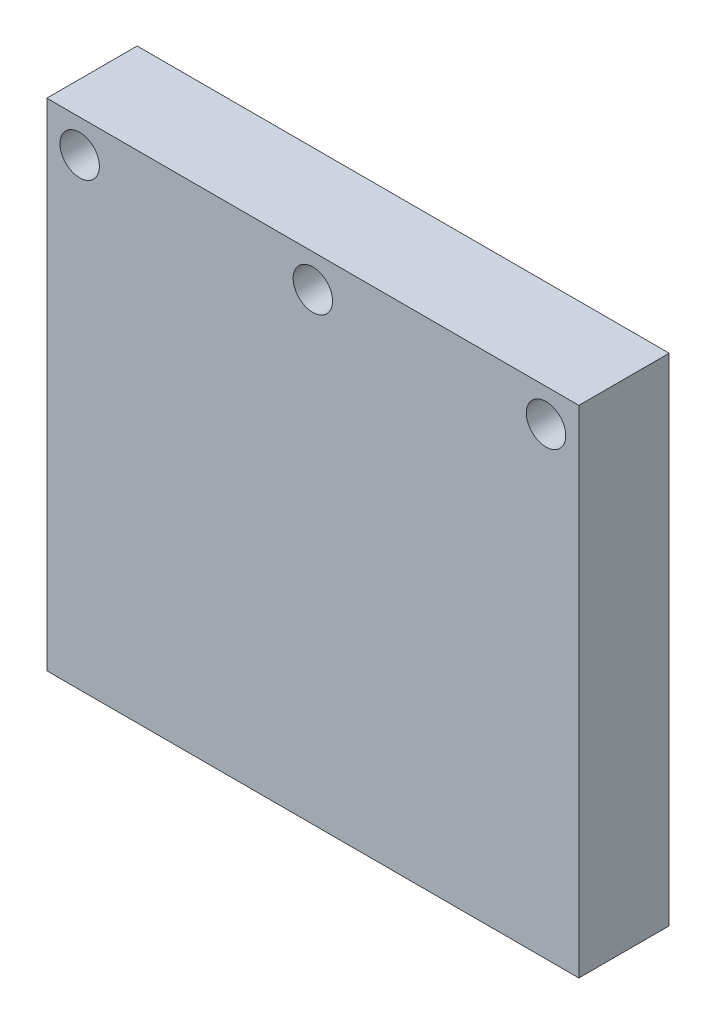
SolidWorks part; units mm, degrees
material "grey resin"
ref_plane "Front Plane" through (0, 0, 0) normal (0, 0, 1) x (1, 0, 0)
ref_plane "Top Plane" through (0, 0, 0) normal (0, 1, 0) x (1, 0, 0)
ref_plane "Right Plane" through (0, 0, 0) normal (1, 0, 0) x (0, 0, -1)
sketch "Sketch1" plane through (0, 0, 0) normal (0, 0, 1) x (1, 0, 0)
  line L0 (0, 7.55) -> (0, -7.55) construction
  line L1 (-8.1, 7.55) -> (8.1, 7.55)
  line L2 (-8.1, 7.55) -> (-8.1, -7.55)
  line L3 (-8.1, -7.55) -> (8.1, -7.55)
  line L4 (8.1, 7.55) -> (8.1, -7.55)
  line L5 (-8.1, 7.55) -> (8.1, -7.55) construction
  line L6 (-8.1, -7.55) -> (8.1, 7.55) construction
  point P0 (0, 0)
  point P8 (0, 6.55)
  dimension "D1" = 16.2
  dimension "D2" = 15.1
  dimension "D3" = 1
extrude "Boss-Extrude1" add sketch "Sketch1" along normal blind 2.75
hole_wizard "M1 Clearance Hole1" positions "Sketch2" profile "Sketch3" hole size "M1" standard "JIS"
sketch "Sketch2" plane through (0, 0, 2.75) normal (0, 0, 1) x (1, 0, 0)
  line L0 (8.1, -7.55) -> (8.1, 7.55) construction
  line L1 (8.1, 7.55) -> (-8.1, 7.55) construction
  point P0 (7.1, 6.55)
  dimension "D1" = 1
  dimension "D2" = 1
sketch "Sketch3" plane through (7.1, 6.55, 2.75) normal (1, 0, 0) x (0, -1, 0)
  line L0 (0, 0) -> (0, 3.5105)
  line L1 (0, 3.5105) -> (0.6, 3.15)
  line L2 (0.6, 3.15) -> (0.6, 0)
  line L5 (0.6, 0) -> (0, 0)
  line L10 (0, 3.5105) -> (-0.6, 3.15) construction
  line L11 (0, -6.35) -> (0, 107.95) construction
  dimension "Hole Dia." = 1.2
  dimension "Hole Depth" = 3.15
  dimension "Drill Angle" = 118
mirror "Mirror1" about plane through (0, 0, 0) normal (1, 0, 0) of "M1 Clearance Hole1"
hole_wizard "M1 Clearance Hole2" positions "Sketch4" profile "Sketch5" hole size "M1" standard "ISO" end condition up to next
sketch "Sketch4" plane through (0, 0, 2.75) normal (0, 0, 1) x (1, 0, 0)
  point P0 (0, 6.55)
sketch "Sketch5" plane through (0, 6.55, 2.75) normal (1, 0, 0) x (0, -1, 0)
  line L0 (0, 0) -> (0, 2.75)
  line L1 (0, 2.75) -> (0.6, 2.75)
  line L2 (0.6, 2.75) -> (0.6, 0)
  line L5 (0.6, 0) -> (0, 0)
  line L11 (0, -6.35) -> (0, 107.95) construction
  dimension "Thru Hole Dia." = 1.2
  dimension "Thru Hole Depth" = 2.75
